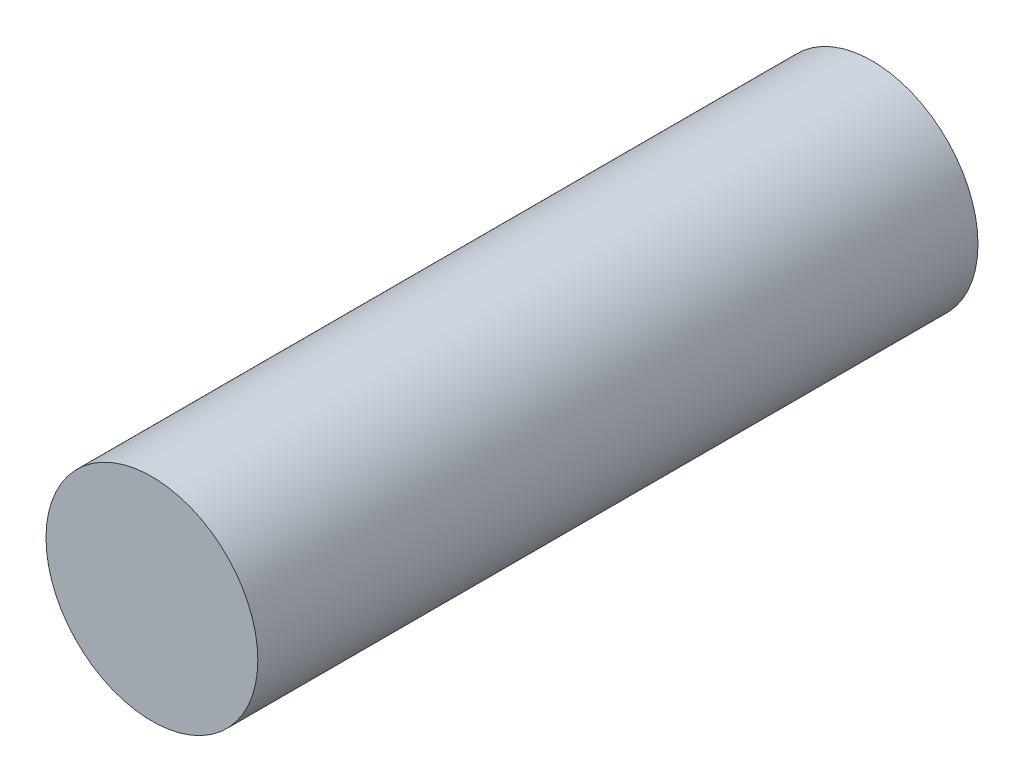
SolidWorks part; units mm, degrees
ref_plane "Front Plane" through (0, 0, 0) normal (0, 0, 1) x (1, 0, 0)
ref_plane "Top Plane" through (0, 0, 0) normal (0, 1, 0) x (1, 0, 0)
ref_plane "Right Plane" through (0, 0, 0) normal (1, 0, 0) x (0, 0, -1)
sketch "Sketch1" plane through (0, 0, 0) normal (0, 0, 1) x (1, 0, 0)
  circle A0 centre (0, 0) radius 25
  dimension "D1" = 50
extrude "Boss-Extrude1" add sketch "Sketch1" along normal blind 170
